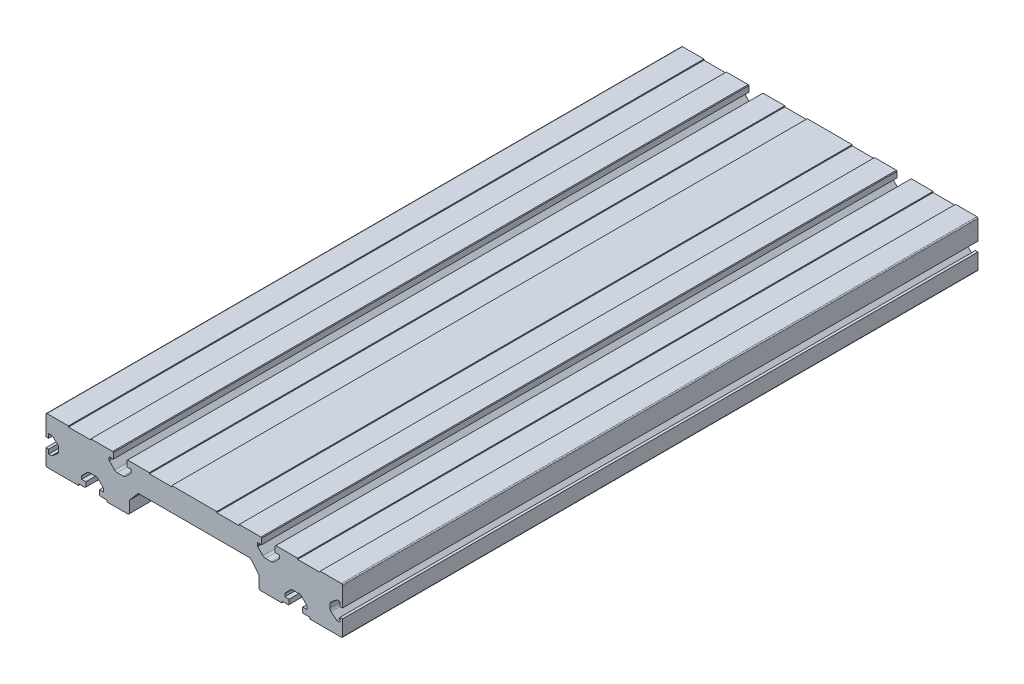
SolidWorks part; units mm, degrees
ref_plane "Ön Düzlem" through (0, 0, 0) normal (0, 0, 1) x (1, 0, 0)
ref_plane "Üst Düzlem" through (0, 0, 0) normal (0, 1, 0) x (1, 0, 0)
ref_plane "Sağ Düzlem" through (0, 0, 0) normal (1, 0, 0) x (0, 0, -1)
sketch "Çizim1" plane through (0, 0, 0) normal (0, 0, 1) x (1, 0, 0)
  line L0 (-2.1019, 10.8881) -> (127.5, 10.8881) construction
  line L1 (0.5, 0) -> (15.3, 0)
  line L2 (0, 0.5) -> (0, 7.8)
  line L3 (0.5, 22) -> (10.6, 22)
  line L4 (48.8, 22) -> (48.8, 21.5)
  line L5 (70, 22) -> (70, -0.381) construction
  line L6 (0, 12.2417) -> (1.25, 12.2417)
  line L7 (1.25, 12.2417) -> (1.25, 14.2417)
  line L8 (1.25, 14.2417) -> (2.568, 14.2417)
  line L9 (2.8894, 14.1247) -> (5.3749, 12.0391)
  line L10 (6, 10.6985) -> (6, 9.3431)
  line L11 (0, 12.2417) -> (0, 21.5)
  line L12 (2.568, 5.8) -> (1.25, 5.8)
  line L13 (1.25, 5.8) -> (1.25, 7.8)
  line L14 (1.25, 7.8) -> (0, 7.8)
  line L15 (22, 0.25) -> (22, 21.5) construction
  line L16 (5.3749, 8.0025) -> (2.8894, 5.917)
  line L17 (15.3, 0) -> (15.3, 0.75)
  line L18 (15.3, 0.75) -> (18.5, 0.75)
  line L19 (18.8, 1.05) -> (18.8, 3.25)
  line L20 (18.8, 3.25) -> (16.8, 3.25)
  line L21 (16.8, 3.25) -> (16.8, 4.5429)
  line L22 (16.9464, 4.8964) -> (19.4018, 7.3518)
  line L23 (20.6393, 7.8644) -> (23.3607, 7.8644)
  line L24 (28.7, 0) -> (28.7, 0.75)
  line L25 (28.7, 0.75) -> (25.5, 0.75)
  line L26 (25.2, 1.05) -> (25.2, 3.25)
  line L27 (25.2, 3.25) -> (27.2, 3.25)
  line L28 (27.2, 3.25) -> (27.2, 4.5429)
  line L29 (27.0536, 4.8964) -> (24.5982, 7.3518)
  line L30 (28.7, 0) -> (38.8823, 0)
  line L31 (35, 14.3856) -> (35, 29.0582) construction
  line L32 (38.5, 22) -> (48.8, 22)
  line L33 (38.2, 21.7) -> (38.2, 19)
  line L34 (48.8, 21.5) -> (59.4, 21.5)
  line L35 (10.6, 22) -> (10.6, 21.5)
  line L36 (21.2, 22) -> (21.2, 21.5)
  line L37 (31.8, 21.7) -> (31.8, 19)
  line L38 (10.6, 21.5) -> (21.2, 21.5)
  line L39 (21.2, 22) -> (31.5, 22)
  line L40 (39.4823, 6.1) -> (39.4823, 22) construction
  line L41 (39.4823, 0.6) -> (39.4823, 6.1)
  line L42 (39.4823, 6.1) -> (43.5, 10.8881)
  line L43 (43.5, 10.8881) -> (96.5, 10.8881)
  line L44 (59.4, 22) -> (59.4, 21.5)
  line L45 (40.0536, 17.3536) -> (37.5982, 14.8982)
  line L46 (40.2, 19) -> (40.2, 17.7071)
  line L47 (38.2, 19) -> (40.2, 19)
  line L48 (59.4, 22) -> (80.6, 22)
  line L49 (31.5, 22) -> (31.8, 21.7)
  line L50 (33.6393, 14.3856) -> (36.3607, 14.3856)
  line L51 (29.9464, 17.3536) -> (32.4018, 14.8982)
  line L52 (29.8, 19) -> (29.8, 17.7071)
  line L53 (31.8, 19) -> (29.8, 19)
  line L54 (38.2, 21.7) -> (38.5, 22)
  line L55 (25.5, 0.75) -> (25.2, 1.05)
  line L56 (18.5, 0.75) -> (18.8, 1.05)
  line L57 (38.8823, 0) -> (39.4823, 0.6)
  line L58 (100.5177, 6.1) -> (100.5177, 22) construction
  line L59 (105, 14.3856) -> (105, 29.0582) construction
  line L60 (118, 0.25) -> (118, 21.5) construction
  line L61 (142.1019, 10.8881) -> (12.5, 10.8881) construction
  line L62 (101.1177, 0) -> (100.5177, 0.6)
  line L63 (121.5, 0.75) -> (121.2, 1.05)
  line L64 (114.5, 0.75) -> (114.8, 1.05)
  line L65 (101.8, 21.7) -> (101.5, 22)
  line L66 (108.2, 19) -> (110.2, 19)
  line L67 (110.2, 19) -> (110.2, 17.7071)
  line L68 (110.0536, 17.3536) -> (107.5982, 14.8982)
  line L69 (106.3607, 14.3856) -> (103.6393, 14.3856)
  line L70 (108.5, 22) -> (108.2, 21.7)
  line L71 (101.8, 19) -> (99.8, 19)
  line L72 (99.8, 19) -> (99.8, 17.7071)
  line L73 (99.9464, 17.3536) -> (102.4018, 14.8982)
  line L74 (80.6, 22) -> (80.6, 21.5)
  line L75 (100.5177, 6.1) -> (96.5, 10.8881)
  line L76 (100.5177, 0.6) -> (100.5177, 6.1)
  line L77 (118.8, 22) -> (108.5, 22)
  line L78 (129.4, 21.5) -> (118.8, 21.5)
  line L79 (108.2, 21.7) -> (108.2, 19)
  line L80 (118.8, 22) -> (118.8, 21.5)
  line L81 (129.4, 22) -> (129.4, 21.5)
  line L82 (91.2, 21.5) -> (80.6, 21.5)
  line L83 (101.8, 21.7) -> (101.8, 19)
  line L84 (101.5, 22) -> (91.2, 22)
  line L85 (111.3, 0) -> (101.1177, 0)
  line L86 (112.9464, 4.8964) -> (115.4018, 7.3518)
  line L87 (112.8, 3.25) -> (112.8, 4.5429)
  line L88 (114.8, 3.25) -> (112.8, 3.25)
  line L89 (114.8, 1.05) -> (114.8, 3.25)
  line L90 (111.3, 0.75) -> (114.5, 0.75)
  line L91 (111.3, 0) -> (111.3, 0.75)
  line L92 (119.3607, 7.8644) -> (116.6393, 7.8644)
  line L93 (123.0536, 4.8964) -> (120.5982, 7.3518)
  line L94 (123.2, 3.25) -> (123.2, 4.5429)
  line L95 (121.2, 3.25) -> (123.2, 3.25)
  line L96 (121.2, 1.05) -> (121.2, 3.25)
  line L97 (124.7, 0.75) -> (121.5, 0.75)
  line L98 (124.7, 0) -> (124.7, 0.75)
  line L99 (134.6251, 8.0025) -> (137.1106, 5.917)
  line L100 (138.75, 7.8) -> (140, 7.8)
  line L101 (138.75, 5.8) -> (138.75, 7.8)
  line L102 (137.432, 5.8) -> (138.75, 5.8)
  line L103 (140, 12.2417) -> (140, 21.5)
  line L104 (134, 10.6985) -> (134, 9.3431)
  line L105 (137.1106, 14.1247) -> (134.6251, 12.0391)
  line L106 (138.75, 14.2417) -> (137.432, 14.2417)
  line L107 (138.75, 12.2417) -> (138.75, 14.2417)
  line L108 (140, 12.2417) -> (138.75, 12.2417)
  line L109 (91.2, 22) -> (91.2, 21.5)
  line L110 (139.5, 22) -> (129.4, 22)
  line L111 (140, 0.5) -> (140, 7.8)
  line L112 (139.5, 0) -> (124.7, 0)
  line L113 (35, 14.3856) -> (35, -19.5934) construction
  line L114 (105, 14.3856) -> (105, -20.589) construction
  arc A0 (6, 9.3431) -> (5.3749, 8.0025) centre (4.25, 9.3431) cw
  arc A1 (6, 10.6985) -> (5.3749, 12.0391) centre (4.25, 10.6985) ccw
  arc A2 (0.5, 0) -> (0, 0.5) centre (0.5, 0.5) cw
  arc A3 (0, 21.5) -> (0.5, 22) centre (0.5, 21.5) cw
  arc A4 (2.8894, 5.917) -> (2.568, 5.8) centre (2.568, 6.3) cw
  arc A5 (2.568, 14.2417) -> (2.8894, 14.1247) centre (2.568, 13.7417) cw
  arc A6 (24.5982, 7.3518) -> (23.3607, 7.8644) centre (23.3607, 6.1144) ccw
  arc A7 (19.4018, 7.3518) -> (20.6393, 7.8644) centre (20.6393, 6.1144) cw
  arc A8 (27.2, 4.5429) -> (27.0536, 4.8964) centre (26.7, 4.5429) ccw
  arc A9 (16.8, 4.5429) -> (16.9464, 4.8964) centre (17.3, 4.5429) cw
  arc A10 (102.4018, 14.8982) -> (103.6393, 14.3856) centre (103.6393, 16.1356) ccw
  arc A11 (107.5982, 14.8982) -> (106.3607, 14.3856) centre (106.3607, 16.1356) cw
  arc A12 (99.8, 17.7071) -> (99.9464, 17.3536) centre (101.3041, 18.123) ccw
  arc A13 (110.2, 17.7071) -> (110.0536, 17.3536) centre (109.7, 17.7071) cw
  arc A14 (29.8, 17.7071) -> (29.9464, 17.3536) centre (30.3, 17.7071) ccw
  arc A15 (40.2, 17.7071) -> (40.0536, 17.3536) centre (38.6959, 18.123) cw
  arc A16 (32.4018, 14.8982) -> (33.6393, 14.3856) centre (33.6393, 16.1356) ccw
  arc A17 (37.5982, 14.8982) -> (36.3607, 14.3856) centre (36.3607, 16.1356) cw
  arc A18 (123.2, 4.5429) -> (123.0536, 4.8964) centre (122.7, 4.5429) ccw
  arc A19 (112.8, 4.5429) -> (112.9464, 4.8964) centre (113.3, 4.5429) cw
  arc A20 (120.5982, 7.3518) -> (119.3607, 7.8644) centre (119.3607, 6.1144) ccw
  arc A21 (115.4018, 7.3518) -> (116.6393, 7.8644) centre (116.6393, 6.1144) cw
  arc A22 (137.432, 14.2417) -> (137.1106, 14.1247) centre (137.432, 13.7417) ccw
  arc A23 (137.1106, 5.917) -> (137.432, 5.8) centre (137.432, 6.3) ccw
  arc A24 (140, 21.5) -> (139.5, 22) centre (139.5, 21.5) ccw
  arc A25 (139.5, 0) -> (140, 0.5) centre (139.5, 0.5) ccw
  arc A26 (134, 10.6985) -> (134.6251, 12.0391) centre (135.75, 10.6985) cw
  arc A27 (134, 9.3431) -> (134.6251, 8.0025) centre (135.75, 9.3431) ccw
  point P25 (0, 0)
  point P28 (0, 22)
  point P31 (2.75, 5.8)
  point P34 (2.75, 14.2417)
  point P40 (18.8, 0.75)
  point P47 (25.2, 0.75)
  point P52 (22, 10.8881)
  point P54 (27.1353, 10.8881)
  point P57 (16.8647, 10.8881)
  point P60 (27.2, 4.75)
  point P63 (16.8, 4.75)
  point P73 (38.2, 22)
  point P74 (31.8, 22)
  point P75 (39.4823, 0)
  point P172 (70, 10.8881)
  point P192 (100.5177, 0)
  point P193 (108.2, 22)
  point P194 (101.8, 22)
  point P195 (123.2, 4.75)
  point P196 (112.8, 4.75)
  point P197 (123.1353, 10.8881)
  point P198 (112.8647, 10.8881)
  point P199 (118, 10.8881)
  point P200 (114.8, 0.75)
  point P201 (121.2, 0.75)
  point P202 (137.25, 14.2417)
  point P203 (137.25, 5.8)
  point P204 (140, 22)
  point P205 (140, 0)
  dimension "D9" = 1.75
  dimension "D13" = 1.75
  dimension "D14" = 0.5
  dimension "D15" = 0.5
  dimension "D25" = 1.75
  dimension "D26" = 0.5
  dimension "D28" = 70
  dimension "D34" = 10.6
  dimension "D35" = 140
  dimension "D37" = 5.5
  dimension "D42" = 2
  dimension "D3" = 6
  dimension "D4" = 140
  dimension "D5" = 1.25
  dimension "D6" = 1.25
  dimension "D7" = 2
  dimension "D8" = 2
  dimension "D10" = 2.5
  dimension "D11" = 1.5
  dimension "D12" = 1.5
  dimension "D16" = 140
  dimension "D17" = 22
  dimension "D18" = 0.75
  dimension "D19" = 3.5
  dimension "D20" = 2.5
  dimension "D21" = 2
  dimension "D22" = 1.5
  dimension "D23" = 45
  dimension "D24" = 3.2
  dimension "D27" = 45
  dimension "D29" = 3
  dimension "D30" = 0.5
  dimension "D31" = 10.6
  dimension "D32" = 6.4
  dimension "D33" = 10.6
  dimension "D36" = 26.5
  dimension "D38" = 22
  dimension "D39" = 35
  dimension "D40" = 0.5
  dimension "D41" = 10.6
  dimension "D43" = 2
  dimension "D44" = 10.6
extrude "Yükseklik-Ekstrüzyon1" add sketch "Çizim1" along normal blind 300 contours L37 L53 L52 A14 L51 A16 L50 A17 L45 A15 L46 L47 L33 L54 L32 L4 L34 L44 L48 L74 L82 L109 L84 L65 L83 L71 L72 A12 L73 A10 L69 A11 L68 A13 L67 L66 L79 L70 L77 L80 L78 L81 L110 A24 L103 L108 L107 L106 A22 L105 A26 L104 A27 L99 A23 L102 L101 L100 L111 A25 L112 L98 L97 L63 L96 L95 L94 A18 L93 A20 L92 A21 L86 A19 L87 L88 L89 L64 L90 L91 L85 L62 L76 L75 L43 L42 L41 L57 L30 L24 L25 L55 L26 L27 L28 A8 L29 A6 L23 A7 L22 A9 L21 L20 L19 L56 L18 L17 L1 A2 L2 L14 L13 L12 A4 L16 A0 L10 A1 L9 A5 L8 L7 L6 L11 A3 L3 L35 L38 L36 L39 L49
sketch "Çizim2" plane through (0, 0.75, 0) normal (0, -1, 0) x (1, 0, 0)
  line L0 (22, 300) -> (22, 0) construction
  line L1 (20.6393, 300) -> (23.3607, 300) construction
  line L2 (20.6393, 0) -> (23.3607, 0) construction
  line L3 (118, 300) -> (118, 0) construction
  line L4 (119.3607, 300) -> (116.6393, 300) construction
  line L5 (119.3607, 0) -> (116.6393, 0) construction
